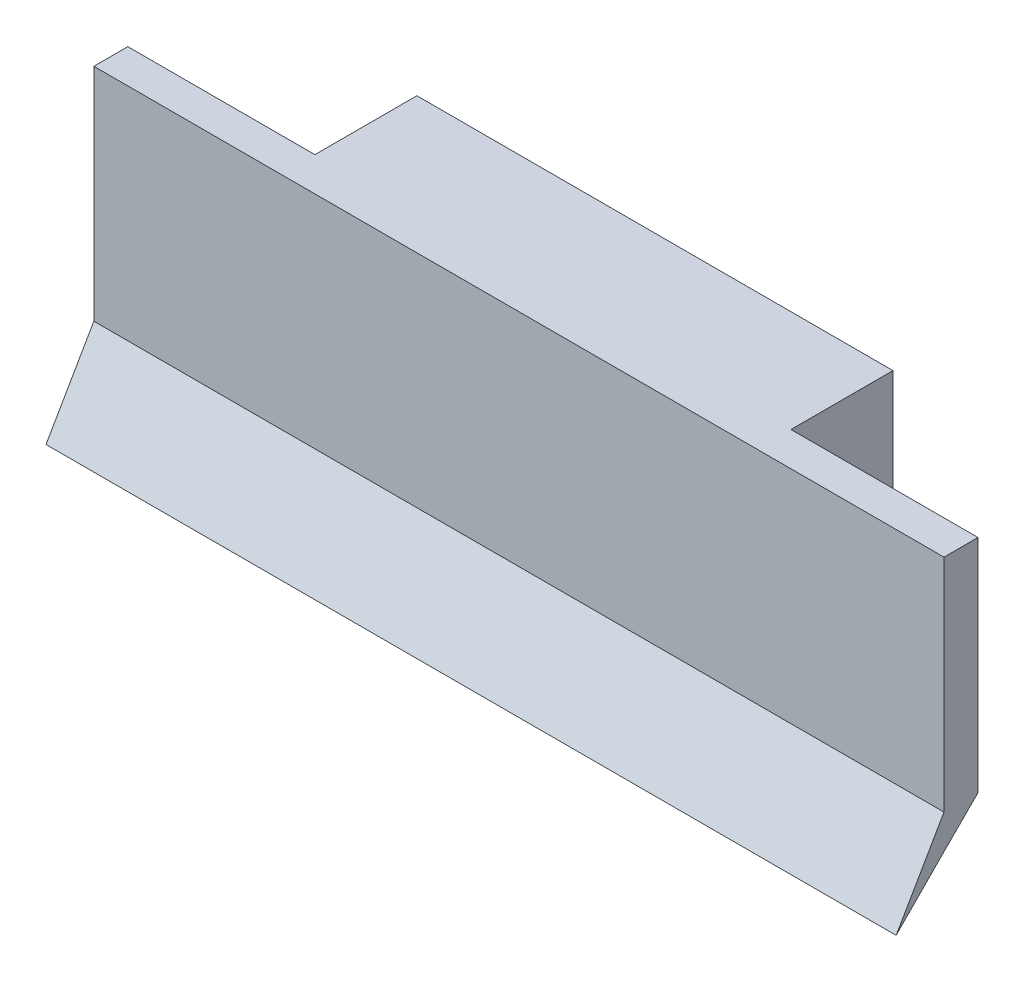
SolidWorks part; units mm, degrees
material "1060 Alloy"
ref_plane "Front Plane" through (0, 0, 0) normal (0, 0, 1) x (1, 0, 0)
ref_plane "Top Plane" through (0, 0, 0) normal (0, 1, 0) x (1, 0, 0)
ref_plane "Right Plane" through (0, 0, 0) normal (1, 0, 0) x (0, 0, -1)
sketch "Sketch1" plane through (0, 0, 0) normal (1, 0, 0) x (0, 0, -1)
  line L0 (-28.9222, -13.4796) -> (-28.9222, 1.5204)
  line L1 (-28.9222, 1.5204) -> (-20.9222, 1.5204)
  line L2 (-20.9222, 1.5204) -> (-20.9222, -5.4796)
  line L3 (-28.9222, -13.4796) -> (-20.9222, -5.4796)
extrude "Boss-Extrude1" add sketch "Sketch1" along normal blind 50
sketch "Sketch2" plane through (50, 0, 0) normal (1, 0, 0) x (0, 0, -1)
  line L0 (-20.9222, 1.5204) -> (-26.9222, 1.5204)
  line L1 (-20.9222, 1.5204) -> (-28.9222, 1.5204) construction
  line L2 (-26.9222, 1.5204) -> (-26.9222, -11.4796)
  line L3 (-28.9222, -13.4796) -> (-20.9222, -5.4796) construction
  line L4 (-20.9222, 1.5204) -> (-20.9222, -5.4796)
  line L5 (-20.9222, -5.4796) -> (-20.9222, 1.5204) construction
  line L6 (-26.9222, -11.4796) -> (-20.9222, -5.4796)
extrude "Cut-Extrude1" cut sketch "Sketch2" against normal blind 11
ref_plane "Plane1" through (25, 0, 0) normal (1, 0, 0) x (0, 0, -1)
mirror "Mirror1" about plane through (25, 0, 0) normal (1, 0, 0) of "Cut-Extrude1"
sketch "Sketch3" plane through (50, 0, 0) normal (1, 0, 0) x (0, 0, -1)
  line L0 (-28.9222, -13.4796) -> (-31.7356, -16.3371)
  line L1 (-31.7356, -16.3371) -> (-28.9222, -11.4642)
  line L4 (-28.9222, 1.5204) -> (-28.9222, -13.4796) construction
  line L5 (-28.9222, -11.4642) -> (-28.9222, -13.4796)
extrude "Boss-Extrude2" add sketch "Sketch3" against normal through all
